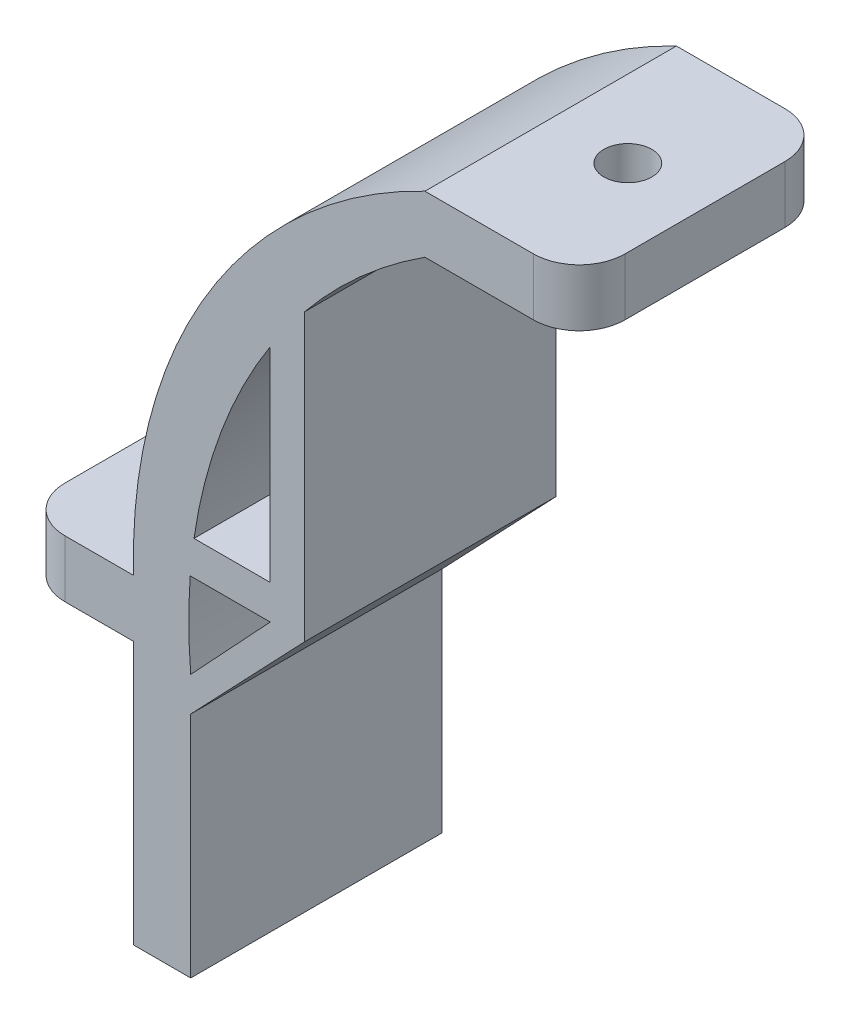
SolidWorks part; units mm, degrees
ref_plane "Front Plane" through (0, 0, 0) normal (0, 0, 1) x (1, 0, 0)
ref_plane "Top Plane" through (0, 0, 0) normal (0, 1, 0) x (1, 0, 0)
ref_plane "Right Plane" through (0, 0, 0) normal (1, 0, 0) x (0, 0, -1)
sketch "Sketch3" plane through (0, 0, 0) normal (0, 0, 1) x (1, 0, 0)
  line L5 (8.4348, 262.2647) -> (-5.0652, 262.2647)
  line L6 (8.4348, 262.2647) -> (8.4348, 257.2647)
  line L7 (8.4348, 257.2647) -> (-5.0652, 257.2647)
  line L8 (-5.0652, 262.2647) -> (-5.0652, 257.2647)
  line L9 (-40.5516, 215.4144) -> (-30.5516, 215.4144)
  line L10 (-40.5516, 215.4144) -> (-40.5516, 220.4144)
  line L11 (-40.5516, 220.4144) -> (-30.5516, 220.4144)
  line L12 (-30.5516, 215.4144) -> (-30.5516, 220.4144)
  line L13 (-30.5516, 215.4144) -> (-25.5516, 215.4144)
  line L14 (-30.5516, 215.4144) -> (-30.5516, 192.4144)
  line L15 (-30.5516, 192.4144) -> (-25.5516, 192.4144)
  line L16 (-25.5516, 215.4144) -> (-25.5516, 192.4144)
  arc A0 (-30.5516, 220.4144) -> (-5.0652, 262.2647) centre (14.4298, 221.7068) cw
  arc A1 (-5.0652, 257.2647) -> (-25.5516, 215.4144) centre (19.2704, 219.4126) ccw
  dimension "D8" = 45
  dimension "D9" = 45
  dimension "D3" = 13.5
  dimension "D4" = 5
  dimension "D6" = 10
  dimension "D7" = 5
extrude "Boss-Extrude1" add sketch "Sketch3" along normal blind 45 contours A1 L8 A0 L12 L13 | L5 L8 L7 L6 | L9 L12 L11 L10 | L16 L13 L14 L15
fillet "Fillet1" radius 2 4 edges at (-40.5516, 217.9144, 0) (-40.5516, 217.9144, 45) (8.4348, 259.7647, 0) (8.4348, 259.7647, 45)
sketch "Sketch5" plane through (0, 262.2647, 0) normal (0, 1, 0) x (1, 0, 0)
  line L0 (-5.0652, -45) -> (-5.0652, 0) construction
  line L2 (6.4348, -45) -> (-5.0652, -45) construction
  circle A0 centre (0.2448, -40) radius 2.1
  circle A2 centre (0.2448, -14.8) radius 2.1
  dimension "D1" = 5.31
  dimension "D2" = 4.2
  dimension "D4" = 5
  dimension "D6" = 4.2
extrude "Cut-Extrude2" cut sketch "Sketch5" against normal blind 45
sketch "Sketch6" plane through (0, 220.4144, 0) normal (0, 1, 0) x (1, 0, 0)
  line L0 (-38.5516, -45) -> (-30.5516, -45) construction
  line L1 (-40.5516, -43) -> (-40.5516, -2) construction
  line L2 (-38.5516, 0) -> (-30.5516, 0) construction
  circle A0 centre (-35.5516, -10) radius 2.1
  circle A1 centre (-35.5516, -35) radius 2.1
  dimension "D1" = 4.2
  dimension "D2" = 4.2
  dimension "D3" = 10
  dimension "D4" = 5
  dimension "D5" = 5
  dimension "D6" = 10
extrude "Cut-Extrude3" cut sketch "Sketch6" against normal blind 45
sketch "Sketch7" plane through (0, 262.2647, 0) normal (0, 1, 0) x (1, 0, 0)
  line L1 (-3.0108, -10.6298) -> (5.1997, -10.6298)
  line L2 (-3.0108, -10.6298) -> (-3.0108, -43.2171)
  line L3 (-3.0108, -43.2171) -> (5.1997, -43.2171)
  line L4 (5.1997, -10.6298) -> (5.1997, -43.2171)
extrude "Boss-Extrude2" add sketch "Sketch7" against normal up to surface (5 mm away) contours L2 L1 L4 L3 up to face at (0.2448, 257.2647, 37.9)
sketch "Sketch8" plane through (0, 262.2647, 0) normal (0, 1, 0) x (1, 0, 0)
  line L0 (-5.0652, -35.2) -> (8.4348, -35.2)
  line L1 (-5.0652, -45) -> (-5.0652, 0) construction
  line L2 (8.4348, -43) -> (8.4348, -2) construction
  line L3 (6.4348, 0) -> (-5.0652, 0) construction
  circle A0 centre (0.2448, -5) radius 2.1
  circle A1 centre (0.2448, -30.2) radius 2.1
  dimension "D1" = 4.2
  dimension "D2" = 4.2
  dimension "D3" = 5
  dimension "D4" = 5
  dimension "D6" = 5.31
  dimension "D7" = 5.31
  dimension "D5" = 35.2
extrude "Cut-Extrude5" cut sketch "Sketch8" against normal blind 45 contours A0 | A1
sketch "Sketch9" plane through (0, 0, 45) normal (0, 0, 1) x (1, 0, 0)
  line L0 (-25.5974, 222.8598) -> (-15.5974, 222.8598)
  line L1 (-15.5974, 222.8598) -> (-15.5974, 247.8598)
  line L2 (-18.5974, 243.7238) -> (-18.5974, 225.8598)
  line L3 (-18.5974, 225.8598) -> (-25.2654, 225.8598)
  line L4 (-15.5974, 222.8598) -> (-25.5516, 212.4144)
  line L5 (-25.5516, 215.4144) -> (-25.5516, 192.4144) construction
  line L6 (-18.5974, 222.8598) -> (-25.5516, 215.4144)
  arc A0 (-5.0652, 257.2647) -> (-25.5516, 215.4144) centre (19.2704, 219.4126) ccw construction
  point P8 (-20.5974, 222.8598)
  line M11 (-25.5516, 192.4144) -> (-25.5516, 215.4144)
  arc M12 (-25.5516, 215.4144) -> (-5.0652, 257.2647) centre (19.2704, 219.4126) cw
  dimension "D1" = 25
  dimension "D2" = 10
  dimension "D3" = 3
  dimension "D4" = 3
  dimension "D5" = 3
extrude "Boss-Extrude3" add sketch "Sketch9" against normal through all contours L2 L3 L0 L1 M12 | L0 L6 L4 M11
sketch "Sketch10" plane through (0, 0, 45) normal (0, 0, 1) x (1, 0, 0)
  line L1 (8.4348, 262.2647) -> (-51.9209, 262.2647)
  line L2 (8.4348, 262.2647) -> (8.4348, 186.8831)
  line L3 (8.4348, 186.8831) -> (-51.9209, 186.8831)
  line L4 (-51.9209, 262.2647) -> (-51.9209, 186.8831)
extrude "Cut-Extrude7" cut sketch "Sketch10" against normal blind 9
sketch "Sketch13" plane through (0, 220.4144, 0) normal (0, 1, 0) x (1, 0, 0)
  line L0 (-30.5516, -36) -> (-33.705, -36) construction
  line L1 (-38.2234, -6.9443) -> (-32.1283, -6.9443)
  line L2 (-38.2234, -6.9443) -> (-38.2234, -36)
  line L3 (-38.2234, -36) -> (-32.1283, -36)
  line L4 (-32.1283, -6.9443) -> (-32.1283, -36)
extrude "Boss-Extrude6" add sketch "Sketch13" against normal up to surface (5 mm away) up to face at (-35.5516, 215.4144, 12.1)
sketch "Sketch14" plane through (0, 262.2647, 0) normal (0, 1, 0) x (1, 0, 0)
  line L1 (-3.0485, -2.0187) -> (3.3761, -2.0187)
  line L2 (-3.0485, -2.0187) -> (-3.0485, -32.8034)
  line L3 (-3.0485, -32.8034) -> (3.3761, -32.8034)
  line L4 (3.3761, -2.0187) -> (3.3761, -32.8034)
extrude "Boss-Extrude7" add sketch "Sketch14" against normal up to surface (5 mm away) up to face at (2.7176, 257.2647, 14.7172)
fillet "Fillet3" radius 2 2 edges at (-40.5516, 217.9144, 36) (8.4348, 259.7647, 36)
sketch "Sketch15" plane through (0, 220.4144, 0) normal (0, 1, 0) x (1, 0, 0)
  line L0 (-38.5516, 0) -> (-30.5516, 0) construction
  line L1 (-40.5516, -34) -> (-40.5516, -2) construction
  line L2 (-30.5516, -36) -> (-38.5516, -36) construction
  circle A0 centre (-35.5516, -8) radius 2.1
  circle A1 centre (-35.5516, -28) radius 2.1
  dimension "D1" = 4.2
  dimension "D2" = 4.2
  dimension "D3" = 8
  dimension "D4" = 5
  dimension "D5" = 5
  dimension "D6" = 8
extrude "Cut-Extrude8" cut sketch "Sketch15" against normal blind 9
sketch "Sketch16" plane through (0, 262.2647, 0) normal (0, 1, 0) x (1, 0, 0)
  line L5 (1.6848, 0) -> (1.6848, -10.1) construction
  line L6 (1.6848, -25.9) -> (1.6848, -30.1) construction
  circle A0 centre (1.6848, -8) radius 2.1
  circle A1 centre (1.6848, -28) radius 2.1
  dimension "D2" = 4.2
  dimension "D3" = 4.2
extrude "Cut-Extrude9" cut sketch "Sketch16" against normal blind 9
sketch "Sketch17" plane through (0, 220.4144, 0) normal (0, 1, 0) x (1, 0, 0)
  line L0 (-40.5516, -34) -> (-40.5516, -2) construction
  line L1 (-40.5516, -2) -> (10.5099, -2)
  line L2 (-40.5516, -2) -> (-40.5516, 4.0054)
  line L3 (-40.5516, 4.0054) -> (10.5099, 4.0054)
  line L4 (10.5099, -2) -> (10.5099, 4.0054)
  line L6 (-40.5516, -14) -> (18.4196, -14)
  line L7 (-40.5516, -14) -> (-40.5516, -49.1208)
  line L8 (-40.5516, -49.1208) -> (18.4196, -49.1208)
  line L9 (18.4196, -14) -> (18.4196, -49.1208)
  circle A0 centre (-35.5516, -8) radius 2.1
  dimension "D1" = 6
  dimension "D2" = 6
extrude "Cut-Extrude10" cut sketch "Sketch17" against normal through all both and the other way through all
sketch "Sketch18" plane through (0, 0, 14) normal (0, 0, 1) x (1, 0, 0)
  line L0 (8.4348, 257.2647) -> (8.4348, 262.2647)
  line L1 (8.4348, 262.2647) -> (-5.0652, 262.2647)
  line L2 (-5.0652, 262.2647) -> (-5.0652, 257.2647)
  line L3 (-5.0652, 257.2647) -> (8.4348, 257.2647)
  line L4 (-40.5516, 220.4144) -> (-30.5516, 220.4144)
  line L5 (-30.5516, 220.4144) -> (-30.5516, 215.4144)
  line L6 (-30.5516, 215.4144) -> (-40.5516, 215.4144)
  line L7 (-40.5516, 215.4144) -> (-40.5516, 220.4144)
  line L8 (-30.5516, 215.4144) -> (-30.5516, 192.4144)
  line L9 (-30.5516, 192.4144) -> (-25.5516, 192.4144)
  line L10 (-25.5516, 192.4144) -> (-25.5516, 212.4144)
  line L11 (-25.5516, 212.4144) -> (-15.5974, 222.8598)
  line L12 (-15.5974, 222.8598) -> (-15.5974, 247.8598)
  line L13 (-18.5974, 243.7238) -> (-18.5974, 225.8598)
  line L14 (-18.5974, 225.8598) -> (-25.2654, 225.8598)
  line L15 (-25.5974, 222.8598) -> (-18.5974, 222.8598)
  line L16 (-18.5974, 222.8598) -> (-25.5516, 215.4144)
  arc A0 (-5.0652, 257.2647) -> (-25.5516, 215.4144) centre (19.2704, 219.4126) ccw
  arc A1 (-5.0652, 262.2647) -> (-30.5516, 220.4144) centre (14.4298, 221.7068) ccw
extrude "Boss-Extrude8" add sketch "Sketch18" along normal blind 5
sketch "Sketch19" plane through (0, 0, 2) normal (0, 0, -1) x (-1, 0, 0)
  line L0 (15.5974, 247.8598) -> (15.5974, 222.8598)
  line L1 (-8.4348, 262.2647) -> (5.0652, 262.2647)
  line L2 (-8.4348, 262.2647) -> (-8.4348, 257.2647)
  line L3 (-8.4348, 257.2647) -> (5.0652, 257.2647)
  line L4 (5.0652, 262.2647) -> (5.0652, 257.2647)
  line L5 (40.5516, 220.4144) -> (30.5516, 220.4144)
  line L6 (40.5516, 220.4144) -> (40.5516, 215.4144)
  line L7 (40.5516, 215.4144) -> (30.5516, 215.4144)
  line L8 (30.5516, 220.4144) -> (30.5516, 215.4144)
  line L9 (15.5974, 222.8598) -> (25.5516, 212.4144)
  line L10 (25.5516, 212.4144) -> (25.5516, 192.4144)
  line L11 (25.5516, 192.4144) -> (30.5516, 192.4144)
  line L12 (30.5516, 192.4144) -> (30.5516, 215.4144)
  line L13 (18.5974, 243.7238) -> (18.5974, 225.8598)
  line L14 (18.5974, 225.8598) -> (25.2654, 225.8598)
  line L15 (25.5516, 215.4144) -> (18.5974, 222.8598)
  line L16 (18.5974, 222.8598) -> (25.5974, 222.8598)
  arc A0 (5.0652, 262.2647) -> (30.5516, 220.4144) centre (-14.4298, 221.7068) cw
  arc A1 (5.0652, 257.2647) -> (25.5516, 215.4144) centre (-19.2704, 219.4126) cw
extrude "Boss-Extrude9" add sketch "Sketch19" along normal blind 5
fillet "Fillet5" radius 4 4 edges at (-40.5516, 217.9144, -3) (-40.5516, 217.9144, 19) (8.4348, 259.7647, 19) (8.4348, 259.7647, -3)
